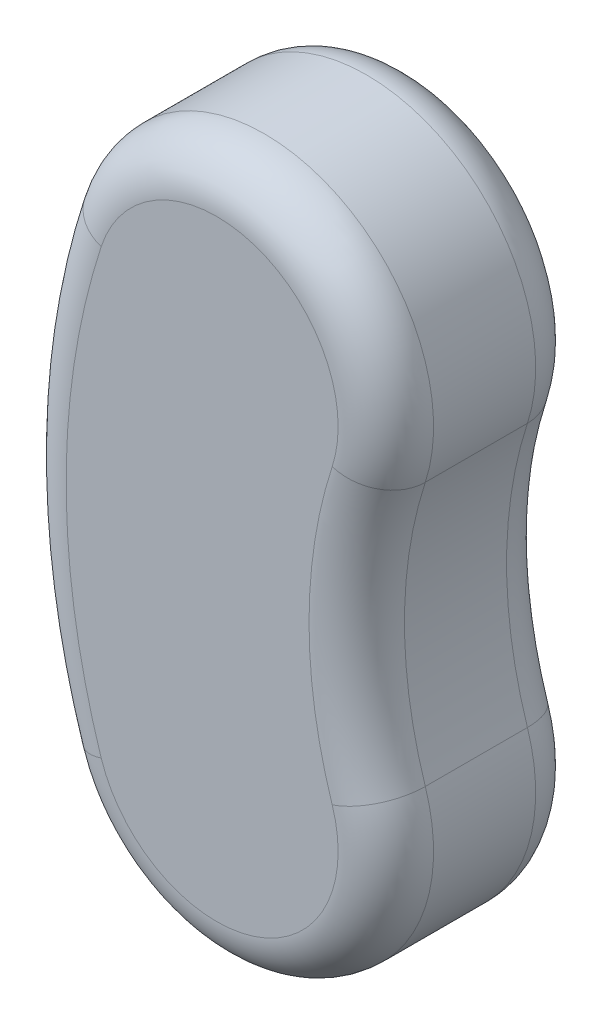
SolidWorks part; units mm, degrees
ref_plane "Front Plane" through (0, 0, 0) normal (1, 0, 0) x (0, 1, 0)
ref_plane "Top Plane" through (0, 0, 0) normal (0, 0, 1) x (0, 1, 0)
ref_plane "Right Plane" through (0, 0, 0) normal (0, 1, 0) x (-1, 0, 0)
sketch "Sketch1" plane through (0, 0, 0) normal (0, 0, 1) x (0, 1, 0)
  line L0 (10.9449, -69.1681) -> (88.0449, -69.1681) construction
  line L1 (49.4949, -63.0681) -> (49.4949, 7.8319) construction
  line L2 (-24.5051, 7.8319) -> (123.4949, 7.8319) construction
  line L3 (-24.5051, 7.8319) -> (-24.5051, 259.4204) construction
  line L4 (123.4949, 7.8319) -> (123.4949, 261.6594) construction
  arc A0 (0, 0) -> (98.9898, 0) centre (49.4949, -152.4798) cw
  arc A1 (21.8898, -67.4362) -> (77.1, -67.4362) centre (49.4949, -152.4798) cw
  arc A2 (21.8898, -67.4362) -> (0, 0) centre (10.9449, -33.7181) cw
  arc A3 (77.1, -67.4362) -> (98.9898, 0) centre (88.0449, -33.7181) ccw
  dimension "D1" = 70.9
  dimension "D2" = 77
  dimension "D3" = 148
extrude "Boss-Extrude1" add sketch "Sketch1" along normal blind 41.4
fillet "Fillet1" radius 10 8 edges at (44.663, -22.7732, 0) (-7.8319, 49.4949, 0) (44.663, 121.763, 0) (44.663, -22.7732, 41.4) (-7.8319, 49.4949, 41.4) (44.663, 121.763, 41.4) (63.0681, 49.4949, 0) (63.0681, 49.4949, 41.4)
